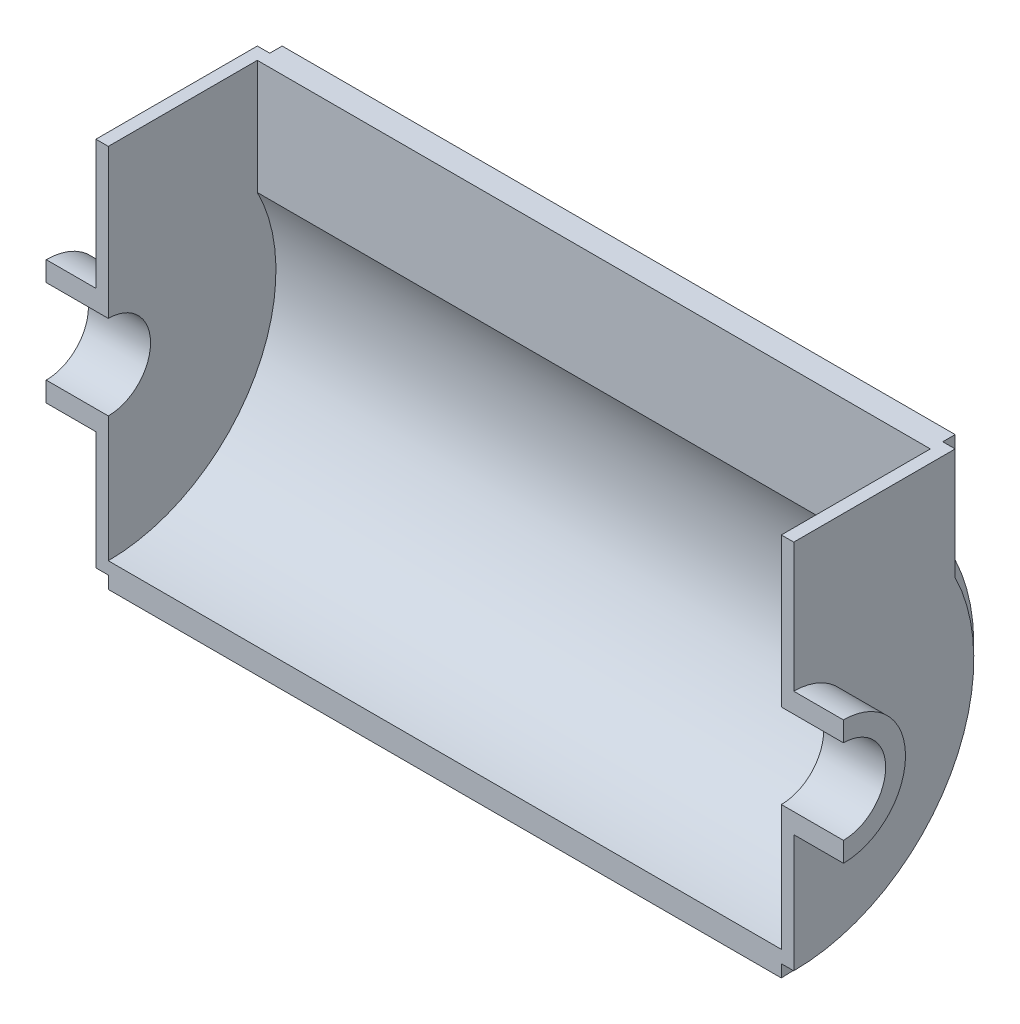
SolidWorks part; units mm, degrees
ref_plane "Ön Düzlem" through (0, 0, 0) normal (0, 0, 1) x (1, 0, 0)
ref_plane "Üst Düzlem" through (0, 0, 0) normal (0, 1, 0) x (1, 0, 0)
ref_plane "Sağ Düzlem" through (0, 0, 0) normal (1, 0, 0) x (0, 0, -1)
sketch "Çizim1" plane through (0, 0, 0) normal (1, 0, 0) x (0, 0, -1)
  line L0 (0, 25) -> (0, 17)
  line L1 (0, -17) -> (0, -25)
  arc A0 (0, -17) -> (0, 17) centre (0, 0) ccw
  arc A1 (0, -25) -> (0, 25) centre (0, 0) ccw
extrude "Yükseklik-Ekstrüzyon1" add sketch "Çizim1" along normal blind 20
sketch "Çizim2" plane through (20, 0, 0) normal (1, 0, 0) x (0, 0, -1)
  line L0 (0, 17) -> (0, 77)
  line L1 (0, 77) -> (65, 77)
  line L2 (65, 77) -> (65, 32.1131)
  line L3 (0, -17) -> (0, -72.5)
  arc A0 (0, -72.5) -> (65, 32.1131) centre (0, 0) ccw
  arc A3 (0, -17) -> (0, 17) centre (0, 0) ccw
extrude "Yükseklik-Ekstrüzyon2" add sketch "Çizim2" along normal blind 5
ref_plane "Düzlem1" through (160.5, 0, 0) normal (1, 0, 0) x (0, 0, -1)
mirror "Aynalama4" about plane through (160.5, 0, 0) normal (1, 0, 0) of bodies 103
sketch "Çizim9" plane through (25, 0, 0) normal (1, 0, 0) x (0, 0, -1)
  line L0 (60, 30.9233) -> (60, 77)
  line L4 (65, 32.1131) -> (65, 77)
  line L5 (65, 77) -> (0, 77)
  line L6 (0, 77) -> (0, 17)
  line L7 (0, -17) -> (0, -72.5)
  line L8 (65, 32.1131) -> (65, 77)
  line L9 (65, 77) -> (0, 77)
  line L10 (0, 77) -> (0, 17)
  line L11 (0, -17) -> (0, -72.5)
  arc A0 (0, -67.5) -> (60, 30.9233) centre (0, 0) ccw
  arc A2 (0, -72.5) -> (65, 32.1131) centre (0, 0) ccw
  arc A3 (0, -17) -> (0, 17) centre (0, 0) ccw
  arc A4 (0, -72.5) -> (65, 32.1131) centre (0, 0) ccw
  arc A5 (0, -17) -> (0, 17) centre (0, 0) ccw
  dimension "D1" = 0
extrude "Ekstrüzyon-İnce4" add sketch "Çizim9" along normal blind 271 thin contours A0 L0
